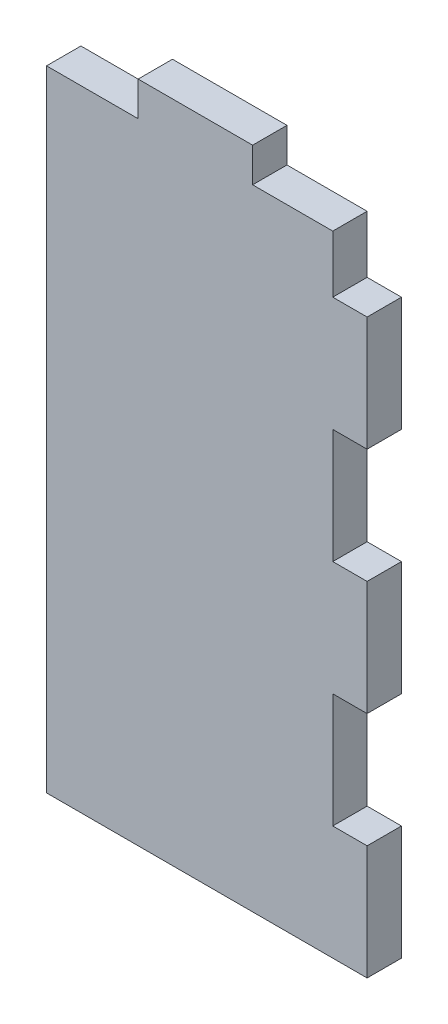
SolidWorks part; units mm, degrees
ref_plane "Plan de face" through (0, 0, 0) normal (0, 0, 1) x (1, 0, 0)
ref_plane "Plan de dessus" through (0, 0, 0) normal (0, 1, 0) x (1, 0, 0)
ref_plane "Plan de droite" through (0, 0, 0) normal (1, 0, 0) x (0, 0, -1)
sketch "Esquisse1" plane through (0, 0, 0) normal (0, 0, 1) x (1, 0, 0)
  line L1 (0, 0) -> (28, 0)
  line L2 (0, 0) -> (0, -58)
  line L3 (0, -58) -> (28, -58)
  line L4 (28, 0) -> (28, -58)
  dimension "D1" = 28
  dimension "D2" = 58
extrude "Boss.-Extru.1" add sketch "Esquisse1" along normal blind 3
sketch "Esquisse2" plane through (0, 0, 3) normal (0, 0, 1) x (1, 0, 0)
  line L0 (28, 0) -> (0, 0) construction
  line L1 (28, 0) -> (18, 0)
  line L2 (28, 0) -> (28, -3)
  line L3 (28, -3) -> (18, -3)
  line L4 (18, 0) -> (18, -3)
  line L6 (28, -58) -> (28, 0) construction
  dimension "D1" = 10
  dimension "D2" = 3
extrude "Enlèv. mat.-Extru.1" cut sketch "Esquisse2" against normal blind 3
pattern_linear "Répétition linéaire1" count 2 spacing 20 along (-1, 0, 0) of "Enlèv. mat.-Extru.1"
sketch "Esquisse3" plane through (0, 0, 3) normal (0, 0, 1) x (1, 0, 0)
  line L0 (28, -58) -> (28, -3) construction
  line L1 (28, -38) -> (25, -38)
  line L2 (28, -38) -> (28, -48)
  line L3 (28, -48) -> (25, -48)
  line L4 (25, -38) -> (25, -48)
  line L5 (0, -58) -> (28, -58) construction
  dimension "D1" = 10
  dimension "D2" = 10
  dimension "D3" = 3
extrude "Enlèv. mat.-Extru.2" cut sketch "Esquisse3" against normal blind 3
pattern_linear "Répétition linéaire2" count 3 spacing 20 along (0, 1, 0) of "Enlèv. mat.-Extru.2"
